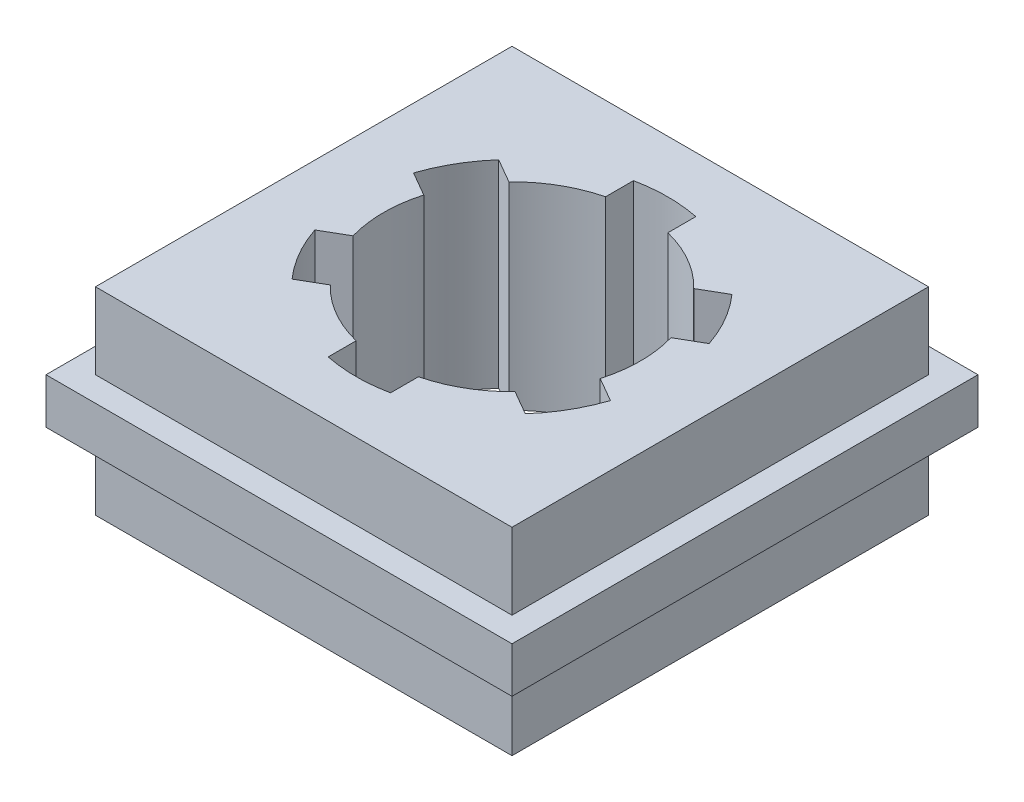
SolidWorks part; units mm, degrees
ref_plane "Front" through (0, 0, 0) normal (0, 0, 1) x (1, 0, 0)
ref_plane "Top" through (0, 0, 0) normal (0, 1, 0) x (1, 0, 0)
ref_plane "Right" through (0, 0, 0) normal (1, 0, 0) x (0, 0, -1)
sketch "Sketch1" plane through (0, 0, 0) normal (0, 1, 0) x (1, 0, 0)
  line L1 (-13.3668, 13.3668) -> (13.3667, 13.3668)
  line L2 (-13.3668, 13.3668) -> (-13.3667, -13.3667)
  line L3 (-13.3667, -13.3667) -> (13.3668, -13.3667)
  line L4 (13.3667, 13.3668) -> (13.3668, -13.3667)
  line L5 (-13.3668, 13.3668) -> (13.3668, -13.3667) construction
  line L6 (-13.3667, -13.3667) -> (13.3667, 13.3668) construction
  point P0 (0, 0)
  dimension "D1" = 26.7335
extrude "Boss-Extrude1" add sketch "Sketch1" along normal mid plane 12.7
sketch "Sketch2" plane through (0, 0, 0) normal (0, 1, 0) x (1, 0, 0)
  line L1 (14.9543, -14.9543) -> (-14.9542, -14.9543)
  line L2 (14.9543, -14.9543) -> (14.9543, 14.9542)
  line L3 (14.9543, 14.9542) -> (-14.9542, 14.9542)
  line L4 (-14.9542, -14.9543) -> (-14.9542, 14.9542)
  line L5 (14.9543, -14.9543) -> (-14.9542, 14.9542) construction
  line L6 (14.9543, 14.9542) -> (-14.9542, -14.9543) construction
  point P0 (0, 0)
  dimension "D1" = 29.9085
extrude "Boss-Extrude2" add sketch "Sketch2" along normal mid plane 2.921
sketch "Sketch3" plane through (0, 6.35, 0) normal (0, 1, 0) x (1, 0, 0)
  line L0 (-2, 9.798) -> (-2, 8.0039)
  line L1 (2, 9.798) -> (2, 8.0039)
  line L2 (7.4853, 6.631) -> (5.9316, 5.734)
  line L3 (9.4853, 3.1669) -> (7.9316, 2.2699)
  line L4 (9.4853, -3.1669) -> (7.9316, -2.2699)
  line L5 (7.4853, -6.631) -> (5.9316, -5.734)
  line L6 (2, -9.798) -> (2, -8.0039)
  line L7 (-2, -9.798) -> (-2, -8.0039)
  line L8 (-7.4853, -6.631) -> (-5.9316, -5.734)
  line L9 (-9.4853, -3.1669) -> (-7.9316, -2.2699)
  line L10 (-9.4853, 3.1669) -> (-7.9316, 2.2699)
  line L11 (-7.4853, 6.631) -> (-5.9316, 5.734)
  arc A0 (-7.4853, 6.631) -> (-9.4853, 3.1669) centre (0, 0) ccw
  arc A1 (-7.9316, 2.2699) -> (-7.9316, -2.2699) centre (0, 0) ccw
  arc A2 (2, 9.798) -> (-2, 9.798) centre (0, 0) ccw
  arc A3 (-2, 8.0039) -> (-5.9316, 5.734) centre (0, 0) ccw
  arc A4 (5.9316, 5.734) -> (2, 8.0039) centre (0, 0) ccw
  arc A5 (9.4853, 3.1669) -> (7.4853, 6.631) centre (0, 0) ccw
  arc A6 (7.9316, -2.2699) -> (7.9316, 2.2699) centre (0, 0) ccw
  arc A7 (7.4853, -6.631) -> (9.4853, -3.1669) centre (0, 0) ccw
  arc A8 (-2, -9.798) -> (2, -9.798) centre (0, 0) ccw
  arc A9 (2, -8.0039) -> (5.9316, -5.734) centre (0, 0) ccw
  arc A10 (-5.9316, -5.734) -> (-2, -8.0039) centre (0, 0) ccw
  arc A11 (-9.4853, -3.1669) -> (-7.4853, -6.631) centre (0, 0) ccw
  point P31 (0, 0)
  dimension "D1" = 20
  dimension "D2" = 16.5
  dimension "D3" = 4
  dimension "D4" = 6
extrude "Cut-Extrude1" cut sketch "Sketch3" against normal through all
